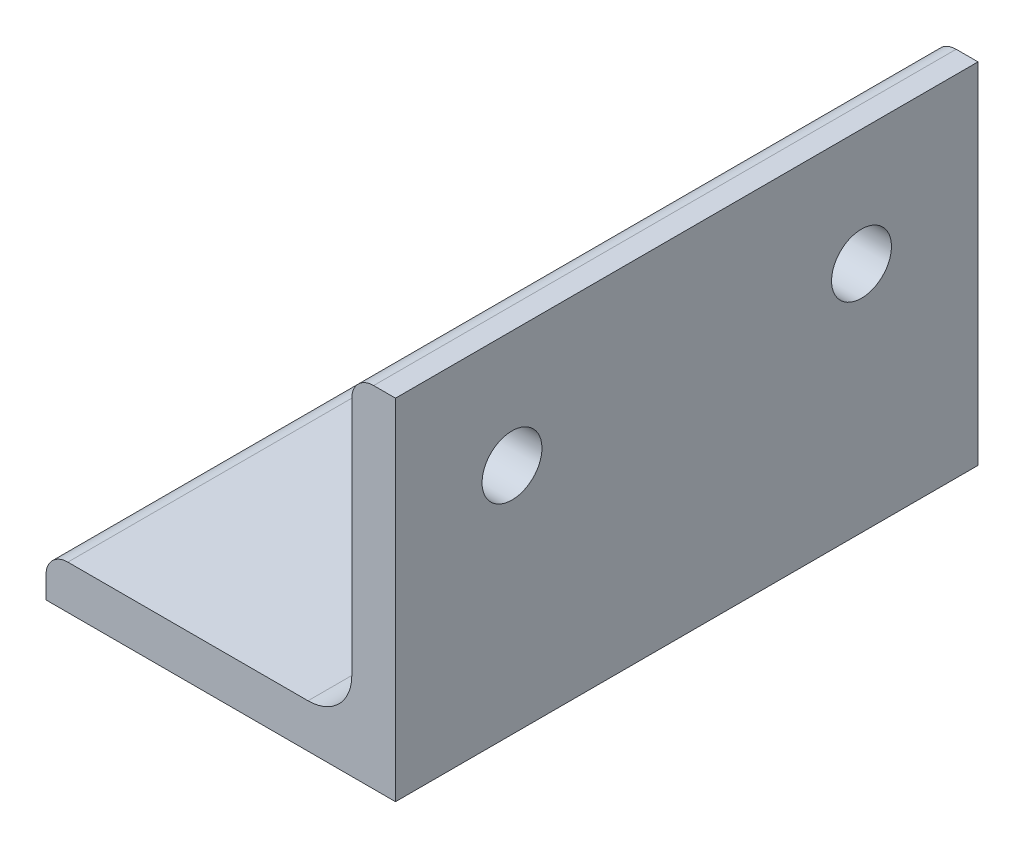
SolidWorks part; units mm, degrees
ref_plane "Front Plane" through (0, 0, 0) normal (0, 0, 1) x (1, 0, 0)
ref_plane "Top Plane" through (0, 0, 0) normal (0, 1, 0) x (1, 0, 0)
ref_plane "Right Plane" through (0, 0, 0) normal (1, 0, 0) x (0, 0, -1)
sketch "Sketch0" plane through (0, 0, 0) normal (0, 0, 1) x (1, 0, 0)
  line L0 (-19.05, -19.05) -> (19.05, -19.05)
  line L1 (19.05, -19.05) -> (19.05, 19.05)
  line L2 (19.05, 0) -> (0, 0) construction
  line L3 (0, 0) -> (0, -19.05) construction
  line L4 (14.2875, -9.5123) -> (14.2875, 19.05) construction
  line L5 (9.5123, -14.2875) -> (-19.05, -14.2875) construction
  arc A0 (14.2875, -9.5123) -> (9.5123, -14.2875) centre (9.5123, -9.5123) cw
  point P3 (12.8889, -12.8889)
  dimension "Inside Corner Radius" = 4.7752
  dimension "Outside Width" = 38.1
  dimension "Wall Thickness" = 4.7625
  dimension "D2" = 4.7625
  dimension "Outside Height" = 38.1
  dimension "Inside Height" = 33.3375
  dimension "Inside Width" = 33.3375
sketch "Sketch1" plane through (0, 0, 0) normal (1, 0, 0) x (0, 0, -1)
  line L0 (152.4, 0) -> (-152.4, 0)
  point P4 (0, 0)
  dimension "Length" = 304.8
sketch "Sketch2" plane through (0, 0, 0) normal (0, 0, 1) x (1, 0, 0)
  line L0 (-19.05, -19.05) -> (19.05, -19.05)
  line L1 (19.05, -19.05) -> (19.05, 19.05)
  line L2 (19.05, 19.05) -> (14.2875, 19.05) construction
  line L3 (14.2875, 16.6688) -> (14.2875, -9.5123)
  line L4 (9.5123, -14.2875) -> (-16.6687, -14.2875)
  line L5 (-19.05, -19.05) -> (-19.05, -14.2875) construction
  line L6 (16.6688, 19.05) -> (19.05, 19.05)
  line L7 (-19.05, -16.6688) -> (-19.05, -19.05)
  line L8 (19.05, 0) -> (0, 0) construction
  line L9 (0, 0) -> (0, -19.05) construction
  arc A0 (14.2875, 16.6688) -> (16.6688, 19.05) centre (16.6688, 16.6688) cw
  arc A1 (-19.05, -16.6688) -> (-16.6687, -14.2875) centre (-16.6687, -16.6688) cw
  arc A2 (14.2875, -9.5123) -> (9.5123, -14.2875) centre (9.5123, -9.5123) cw
  dimension "Inside Radius" = 4.7752
  dimension "Height" = 38.1
  dimension "Width" = 38.1
  dimension "Thickness" = 4.7625
extrude "Boss-Extrude1" add sketch "Sketch2" along normal mid plane 63.5
sketch "Break Locations" plane through (0, 0, 0) normal (1, 0, 0) x (0, 0, -1)
  line L0 (7.112, 0) -> (-7.112, 0)
  line L1 (-31.75, -19.05) -> (-31.75, 19.05) construction
  line L2 (31.75, -19.05) -> (31.75, 19.05) construction
  point P0 (0.635, 0)
  point P1 (-0.635, 0)
  point P10 (0, 0)
  point P11 (-7.112, 0)
  point P13 (7.112, 0)
  dimension "D1" = 32.385
  dimension "D2" = 32.385
  dimension "D3" = 38.862
sketch "Sketch5" plane through (14.2875, 0, 0) normal (-1, 0, 0) x (0, 0, 1)
  circle A0 centre (-19.05, 6.35) radius 3.2639 construction
  circle A1 centre (19.05, 6.35) radius 3.2639 construction
  circle A2 centre (-19.05, 6.35) radius 3.2639
  circle A3 centre (19.05, 6.35) radius 3.2639
extrude "Cut-Extrude1" cut sketch "Sketch5" against normal up to next
equation "\"D1@Break Locations\" = .85 * \"Height@Sketch2\""
equation "\"D2@Break Locations\"=\"D1@Break Locations\""
equation "\"D2@Sketch0\" = \"Wall Thickness@Sketch0\""
equation "\"Thickness@Sketch2\"=\"wall thickness@sketch0\""
equation "\"Height@Sketch2\"=\"outside height@sketch0\""
equation "\"Width@Sketch2\"=\"outside width@sketch0\""
equation "\"Inside Radius@Sketch2\"=\"inside corner radius@sketch0\""
equation "\"D3@Break Locations\"=\"D2@Break Locations\"*1.2"
